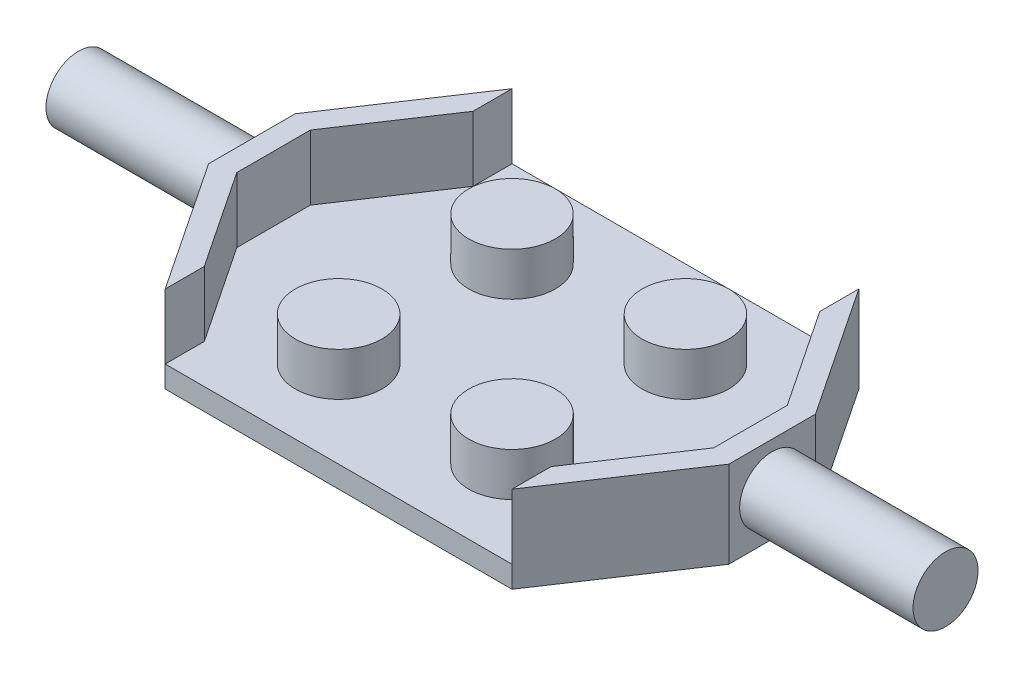
SolidWorks part; units mm, degrees
ref_plane "Front Plane" through (0, 0, 0) normal (0, 0, 1) x (1, 0, 0)
ref_plane "Top Plane" through (0, 0, 0) normal (0, 1, 0) x (1, 0, 0)
ref_plane "Right Plane" through (0, 0, 0) normal (1, 0, 0) x (0, 0, -1)
sketch "Sketch1" plane through (0, 0, 0) normal (0, 1, 0) x (1, 0, 0)
  line L0 (0, 0) -> (0, 8)
  line L1 (0, 0) -> (-12, 0) construction
  line L2 (-12, -2) -> (-12, 2)
  line L3 (0, 8) -> (-8, 8)
  line L4 (-12, 2) -> (-8, 8)
  line L5 (0, -8) -> (-8, -8)
  line L6 (-12, -2) -> (-8, -8)
  line L7 (0, 0) -> (0, -8)
  dimension "D1" = 12
  dimension "D2" = 8
  dimension "D3" = 2
  dimension "D4" = 8
extrude "Boss-Extrude1" add sketch "Sketch1" along normal blind 1
sketch "Sketch2" plane through (0, 1, 0) normal (0, 1, 0) x (1, 0, 0)
  line L0 (0, 8) -> (-8, 8) construction
  line L1 (0, -8) -> (0, 8) construction
  line L2 (-12, 0) -> (0, 0) construction
  line L3 (-12, 2) -> (-12, -2) construction
  circle A0 centre (-4, 4) radius 2
  circle A1 centre (-4, -4) radius 2
  dimension "D1" = 4
  dimension "D2" = 4
  dimension "D3" = 4
extrude "Boss-Extrude2" add sketch "Sketch2" along normal blind 2
sketch "Sketch3" plane through (0, 1, 0) normal (0, 1, 0) x (1, 0, 0)
  line L3 (-12, 2) -> (-12, -2) construction
  line L4 (-12, -2) -> (-8, -8) construction
  line L6 (-12, 2) -> (-12, -2)
  line L7 (-12, -2) -> (-8, -8)
  line L8 (-8, 8) -> (-12, 2) construction
  line L9 (-8, 8) -> (-12, 2)
  line L10 (-8, 6.1972) -> (-11, 1.6972)
  line L11 (-11, 1.6972) -> (-11, -1.6972)
  line L12 (-11, -1.6972) -> (-8, -6.1972)
  line L13 (-8, -8) -> (-8, -6.1972)
  line L14 (-11, -1.6972) -> (-7.1679, -7.4453) construction
  line L15 (-8, 6.1972) -> (-8, 8)
  line L16 (-7.1679, 7.4453) -> (-11, 1.6972) construction
  dimension "D1" = 1
extrude "Boss-Extrude3" add sketch "Sketch3" along normal blind 3
sketch "Sketch4" plane through (-12, 0, 0) normal (-1, 0, 0) x (0, 0, 1)
  line L0 (0, 4) -> (0, 0) construction
  line L1 (-2, 4) -> (2, 4) construction
  circle A0 centre (0, 2) radius 1.5
  dimension "D1" = 3
extrude "Boss-Extrude4" add sketch "Sketch4" along normal blind 8
mirror "Mirror1" about plane through (0, 0, 0) normal (1, 0, 0) of "Boss-Extrude4", "Boss-Extrude2", "Boss-Extrude3", "Boss-Extrude1"
